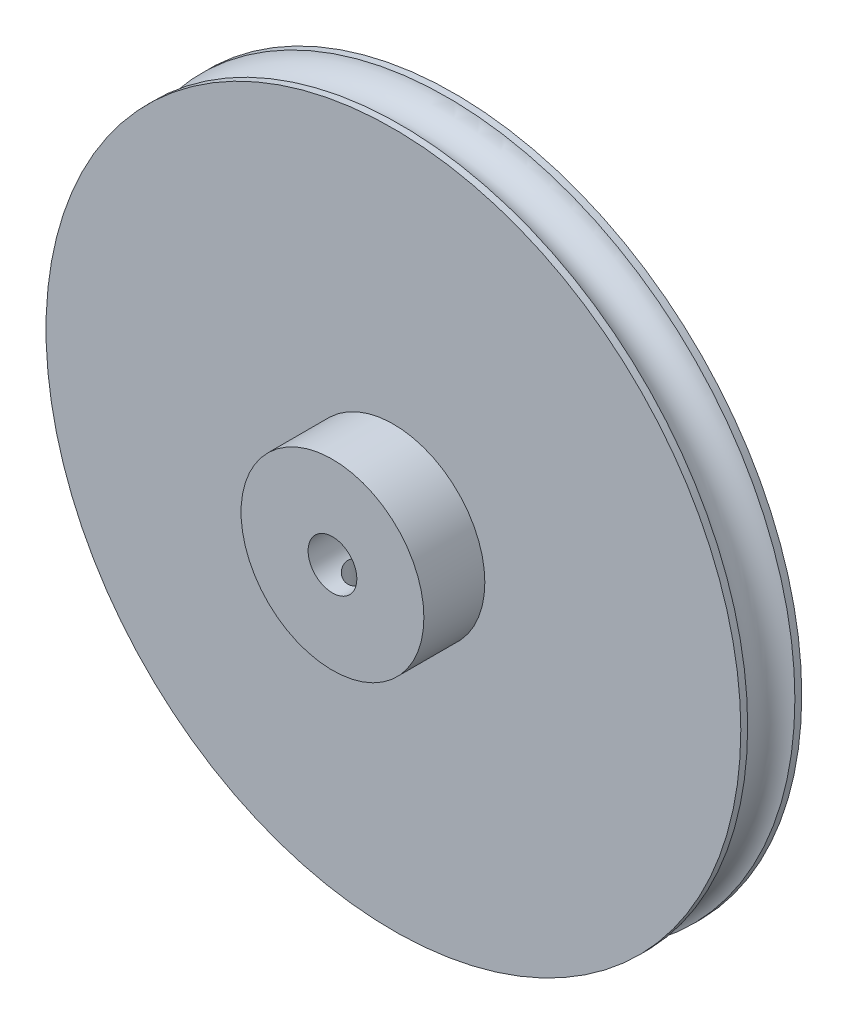
SolidWorks part; units mm, degrees
ref_plane "Plan de face" through (0, 0, 0) normal (0, 0, 1) x (1, 0, 0)
ref_plane "Plan de dessus" through (0, 0, 0) normal (0, 1, 0) x (1, 0, 0)
ref_plane "Plan de droite" through (0, 0, 0) normal (1, 0, 0) x (0, 0, -1)
sketch "Esquisse1" plane through (0, 0, 0) normal (0, 0, 1) x (1, 0, 0)
  circle A0 centre (0, 0) radius 28.5
  dimension "D1" = 57
extrude "Extrusion1" add sketch "Esquisse1" against normal blind 5
sketch "Esquisse2" plane through (0, 0, 0) normal (0, 0, 1) x (1, 0, 0)
  circle A0 centre (0, 0) radius 7.5
  dimension "D1" = 15
extrude "Extrusion2" add sketch "Esquisse2" along normal blind 5
sketch "Esquisse3" plane through (0, 0, 5) normal (0, 0, 1) x (1, 0, 0)
  circle A0 centre (0, 0) radius 2
  dimension "D1" = 4
extrude "Extrusion3" cut sketch "Esquisse3" against normal up to next
sketch "Esquisse6" plane through (0, 0, 0) normal (0, 1, 0) x (1, 0, 0)
  line L0 (-29, 2.5) -> (-27, 2.5) construction
  line L1 (-29, 4.5) -> (-31.4496, 4.5)
  line L2 (-29, 0.5) -> (-31.4496, 0.5)
  line L3 (-28.5, 0) -> (28.5, 0) construction
  line L4 (-29, 0) -> (-29, 0.5) construction
  line L5 (-29, 5) -> (-29, 4.5) construction
  line L6 (28.5, 5) -> (-28.5, 5) construction
  line L7 (-31.4496, 0.5) -> (-31.4496, 4.5)
  line L8 (-29, 0.5) -> (-29, 2.5) construction
  arc A0 (-29, 0.5) -> (-29, 4.5) centre (-29, 2.5) ccw
  dimension "D1" = 2
  dimension "D2" = 0.5
  dimension "D3" = 27
revolve "Enlèvement de matière-Révolution3" cut sketch "Esquisse6" angle 360 about axis through (0, 0, 5) along (0, 0, -1)
ref_plane "Plan1" through (0, 0, 0) normal (0, 1, 0) x (1, 0, 0)
sketch "Esquisse11" plane through (0, 0, 0) normal (0, 1, 0) x (1, 0, 0)
  line L0 (0, 0) -> (0, -5) construction
  line L1 (-7.5, -5) -> (7.5, -5) construction
  point P5 (0, -2.5)
hole_wizard "Trou taraudé M3x0.55" positions "Esquisse13" profile "Esquisse12" tap size "M3x0.5" standard "Ansi Metric"
sketch "Esquisse13" plane through (0, 0, 0) normal (0, 1, 0) x (1, 0, 0)
  line L0 (0, 0) -> (0, -5) construction
  point P8 (0, -2.5)
sketch "Esquisse12" plane through (0, 0, 2.5) normal (1, 0, 0) x (0, 0, 1)
  line L0 (0, 0) -> (0, 28.5)
  line L1 (0, 28.5) -> (1.25, 28.5)
  line L2 (1.25, 28.5) -> (1.25, 0)
  line L5 (1.25, 0) -> (0, 0)
  line L11 (0, -6.35) -> (0, 107.95) construction
  dimension "Diamètre du trou pour taraudage jusqu'au prochain" = 2.5
  dimension "Profondeur du trou pour taraudage jusqu'au prochain" = 28.5
cosmetic thread "Filetage de perçage1" parameters "D2"=3
